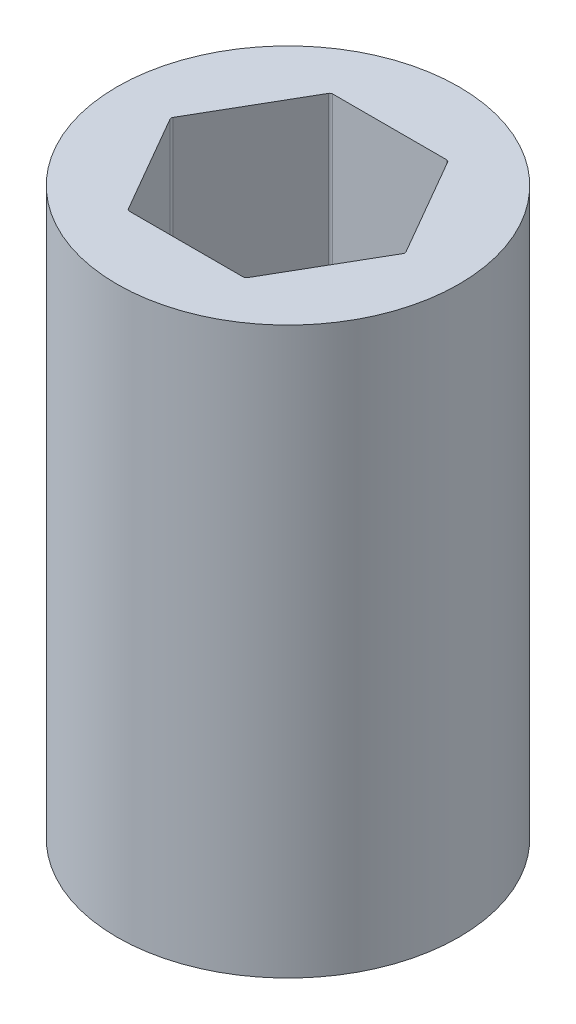
SolidWorks part; units mm, degrees
material "Nylon 101"
ref_plane "Front Plane" through (0, 0, 0) normal (0, 0, 1) x (1, 0, 0)
ref_plane "Top Plane" through (0, 0, 0) normal (0, 1, 0) x (1, 0, 0)
ref_plane "Right Plane" through (0, 0, 0) normal (1, 0, 0) x (0, 0, -1)
sketch "Sketch1" plane through (0, 0, 0) normal (0, 1, 0) x (1, 0, 0)
  line L1 (7.6256, 0) -> (3.8128, 6.604)
  line L2 (3.8128, 6.604) -> (-3.8128, 6.604)
  line L3 (-3.8128, 6.604) -> (-7.6256, 0)
  line L4 (-7.6256, 0) -> (-3.8128, -6.604)
  line L5 (-3.8128, -6.604) -> (3.8128, -6.604)
  line L6 (3.8128, -6.604) -> (7.6256, 0)
  circle A0 centre (0, 0) radius 11.1125
  circle A1 centre (0, 0) radius 6.604 construction
  dimension "D1" = 13.208
  dimension "D2" = 22.225
extrude "Boss-Extrude1" add sketch "Sketch1" along normal blind 36.7538
fillet "Fillet1" radius 0.2 6 edges at (3.8128, 18.3769, -6.604) (-3.8128, 18.3769, -6.604) (-7.6256, 18.3769, 0) (3.8128, 18.3769, 6.604) (7.6256, 18.3769, 0) (-3.8128, 18.3769, 6.604)
